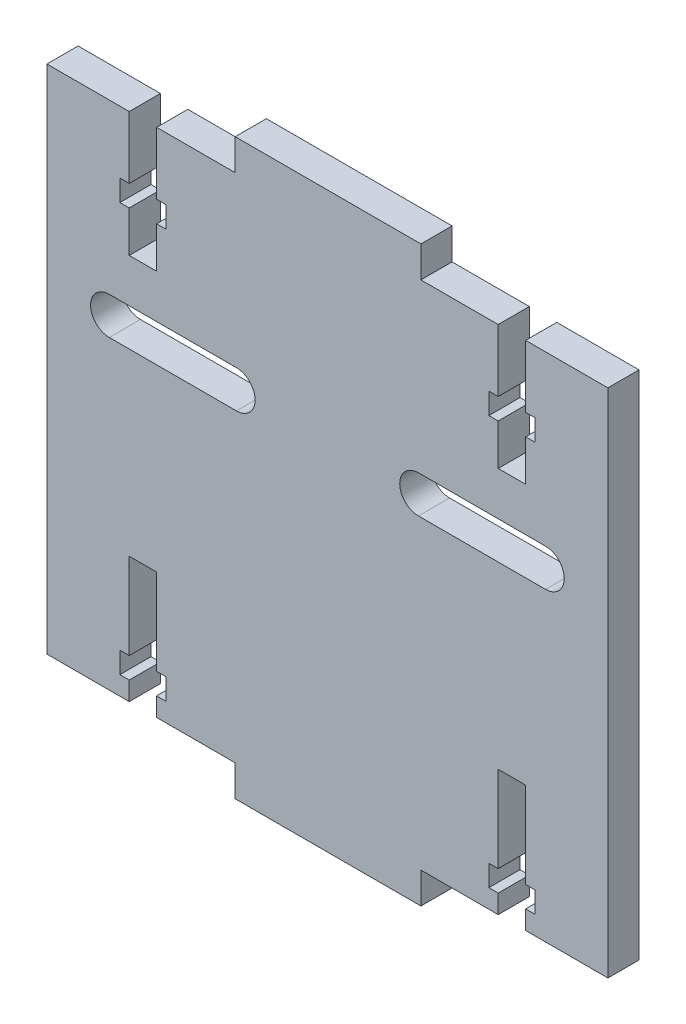
SolidWorks part; units mm, degrees
ref_plane "Front Plane" through (0, 0, 0) normal (0, 0, 1) x (1, 0, 0)
ref_plane "Top Plane" through (0, 0, 0) normal (0, 1, 0) x (1, 0, 0)
ref_plane "Right Plane" through (0, 0, 0) normal (1, 0, 0) x (0, 0, -1)
sketch "Sketch1" plane through (0, 0, 0) normal (0, 0, 1) x (1, 0, 0)
  line L1 (-45, 41) -> (45, 41)
  line L2 (-45, 41) -> (-45, -41)
  line L3 (-45, -41) -> (45, -41)
  line L4 (45, 41) -> (45, -41)
  dimension "D1" = 90
  dimension "D2" = 82
  dimension "D3" = 45
  dimension "D4" = 41
extrude "Boss-Extrude1" add sketch "Sketch1" along normal blind 5
sketch "Sketch4" plane through (0, 0, 5) normal (0, 0, 1) x (1, 0, 0)
  line L0 (45, -41) -> (45, 41) construction
  line L1 (15, 41) -> (-14.8, 41)
  line L2 (15, 41) -> (15, 46)
  line L3 (15, 46) -> (-14.8, 46)
  line L4 (-14.8, 41) -> (-14.8, 46)
  line L5 (45, 41) -> (-45, 41) construction
  dimension "D1" = 30
  dimension "D2" = 5
  dimension "D3" = 29.8
extrude "Boss-Extrude2" add sketch "Sketch4" against normal blind 5
ref_plane "Plane1" through (0, 0, 0) normal (0, -1, 0) x (-1, 0, 0)
mirror "Mirror1" about plane through (0, 0, 0) normal (0, -1, 0) of "Boss-Extrude2"
sketch "Sketch5" plane through (0, 0, 5) normal (0, 0, 1) x (1, 0, 0)
  line L0 (0, 0) -> (0, 51.0938) construction
  line L1 (0, 0) -> (63.9395, 0) construction
  line L2 (27.4, 41) -> (27.4, 31)
  line L3 (-45, -41) -> (-14.8, -41) construction
  line L16 (29.6, 41) -> (29.6, 28.1548) construction
  line L18 (31.8, 27.6) -> (31.8, 21)
  line L22 (33.3, 27.6) -> (31.8, 27.6)
  line L23 (33.3, 31) -> (33.3, 27.6)
  line L24 (31.8, 31) -> (33.3, 31)
  line L25 (31.8, 41) -> (27.4, 41)
  line L28 (31.8, 41) -> (31.8, 31)
  line L29 (29.6, -41) -> (29.6, -26.1548) construction
  line L42 (-29.6, -41) -> (-29.6, -26.1548) construction
  line L55 (31.8, 21) -> (27.4, 21)
  line L56 (27.4, 31) -> (25.9, 31)
  line L57 (25.9, 31) -> (25.9, 27.6)
  line L58 (25.9, 27.6) -> (27.4, 27.6)
  line L59 (27.4, 27.6) -> (27.4, 21)
  line L60 (-29.6, 41) -> (-29.6, 28.1548) construction
  line L61 (-27.4, 27.6) -> (-27.4, 21)
  line L62 (-25.9, 27.6) -> (-27.4, 27.6)
  line L63 (-25.9, 31) -> (-25.9, 27.6)
  line L64 (-27.4, 31) -> (-25.9, 31)
  line L65 (-31.8, 21) -> (-27.4, 21)
  line L66 (-31.8, 41) -> (-31.8, 31)
  line L67 (-31.8, 41) -> (-27.4, 41)
  line L68 (-31.8, 31) -> (-33.3, 31)
  line L69 (-33.3, 31) -> (-33.3, 27.6)
  line L70 (-33.3, 27.6) -> (-31.8, 27.6)
  line L71 (-31.8, 27.6) -> (-31.8, 21)
  line L72 (-27.4, 41) -> (-27.4, 31)
  line L73 (-27.4, -38) -> (-27.4, -41)
  line L74 (31.8, -41) -> (31.8, -38)
  line L75 (-31.8, -34.6) -> (-31.8, -20.8)
  line L76 (-25.9, -34.6) -> (-27.4, -34.6)
  line L77 (-25.9, -38) -> (-25.9, -34.6)
  line L78 (-27.4, -38) -> (-25.9, -38)
  line L79 (-33.3, -34.6) -> (-31.8, -34.6)
  line L80 (-33.3, -38) -> (-33.3, -34.6)
  line L81 (-31.8, -38) -> (-33.3, -38)
  line L82 (-31.8, -41) -> (-27.4, -41)
  line L83 (-27.4, -20.8) -> (-27.4, -34.6)
  line L84 (-31.8, -20.8) -> (-27.4, -20.8)
  line L85 (-31.8, -41) -> (-31.8, -38)
  line L86 (45, 41) -> (15, 41) construction
  line L87 (31.8, -20.8) -> (27.4, -20.8)
  line L88 (27.4, -20.8) -> (27.4, -34.6)
  line L89 (31.8, -41) -> (27.4, -41)
  line L90 (31.8, -38) -> (33.3, -38)
  line L91 (33.3, -38) -> (33.3, -34.6)
  line L92 (33.3, -34.6) -> (31.8, -34.6)
  line L93 (27.4, -38) -> (25.9, -38)
  line L94 (25.9, -38) -> (25.9, -34.6)
  line L95 (25.9, -34.6) -> (27.4, -34.6)
  line L96 (31.8, -34.6) -> (31.8, -20.8)
  line L97 (27.4, -38) -> (27.4, -41)
  point P8 (29.6, 21)
  point P63 (-29.6, 21)
  dimension "D1" = 3.4
  dimension "D2" = 2.2
  dimension "D4" = 1.5
  dimension "D5" = 13.8
  dimension "D6" = 3.4
  dimension "D7" = 3
  dimension "D8" = 27.4
  dimension "D9" = 20
  dimension "D10" = 10
  dimension "D11" = 2.2
  dimension "D12" = 4.4
  dimension "D13" = 1.5
  dimension "D14" = 1.5
  dimension "D15" = 27.4
extrude "Cut-Extrude1" cut sketch "Sketch5" against normal blind 10
sketch "Sketch6" plane through (0, 0, 5) normal (0, 0, 1) x (1, 0, 0)
  line L2 (-14.6, 14) -> (-35, 14)
  line L3 (-35, 8) -> (-14.6, 8)
  line L4 (0, 0) -> (0, 16.13) construction
  line L5 (35, 8) -> (14.6, 8)
  line L6 (14.6, 14) -> (35, 14)
  arc A2 (-35, 14) -> (-35, 8) centre (-35, 11) ccw
  arc A3 (-14.6, 8) -> (-14.6, 14) centre (-14.6, 11) ccw
  arc A4 (14.6, 8) -> (14.6, 14) centre (14.6, 11) cw
  arc A5 (35, 14) -> (35, 8) centre (35, 11) cw
extrude "Cut-Extrude2" cut sketch "Sketch6" against normal blind 10
